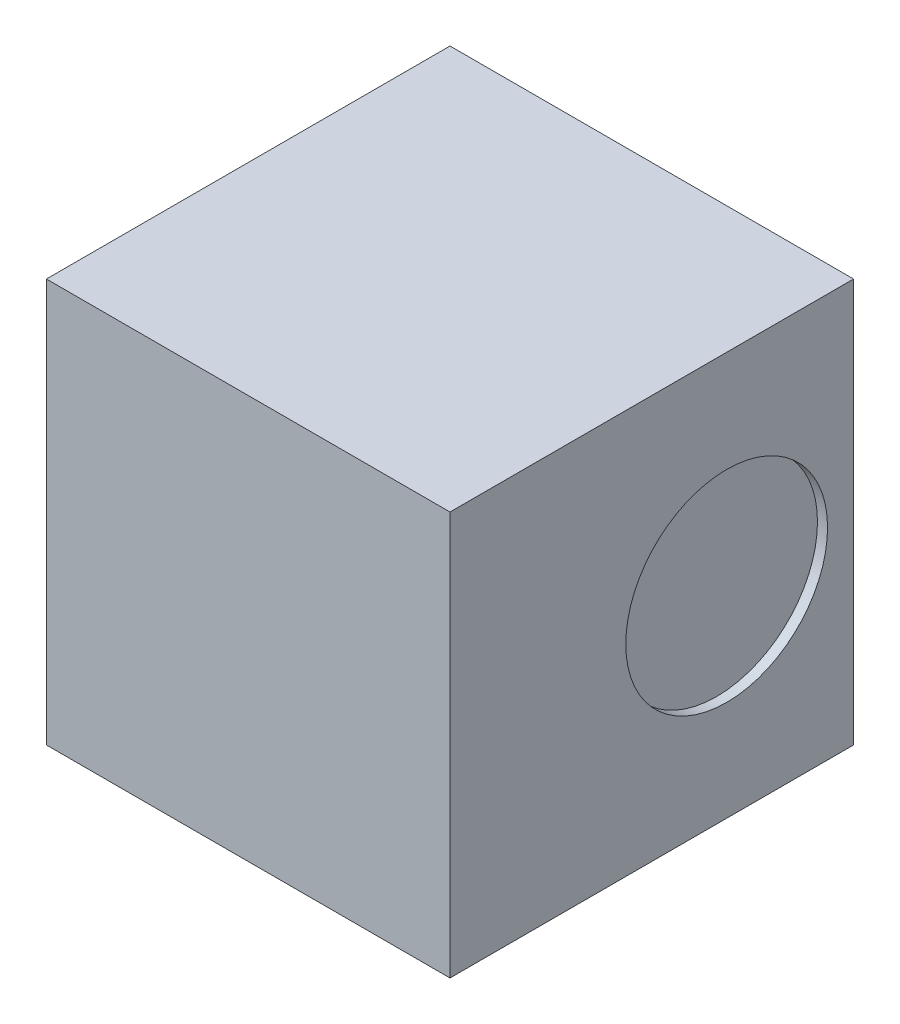
SolidWorks part; units mm, degrees
ref_plane "Front Plane" through (0, 0, 0) normal (0, 0, 1) x (1, 0, 0)
ref_plane "Top Plane" through (0, 0, 0) normal (0, 1, 0) x (1, 0, 0)
ref_plane "Right Plane" through (0, 0, 0) normal (1, 0, 0) x (0, 0, -1)
sketch "Sketch1" plane through (0, 0, 0) normal (0, 1, 0) x (1, 0, 0)
  line L0 (0, 0) -> (18.6879, 0) construction
  line L1 (0, 0) -> (0, -14.4281) construction
  line L3 (-1, 1) -> (1, 1)
  line L4 (-1, 1) -> (-1, -1)
  line L5 (-1, -1) -> (1, -1)
  line L6 (1, 1) -> (1, -1)
  dimension "D1" = 2
extrude "Boss-Extrude1" add sketch "Sketch1" along normal blind 2
sketch "Sketch2" plane through (1, 0, 0) normal (1, 0, 0) x (0, 0, -1)
  circle A1 centre (0.3711, 0.9971) radius 0.5
extrude "Cut-Extrude1" cut sketch "Sketch2" against normal blind 0.05
